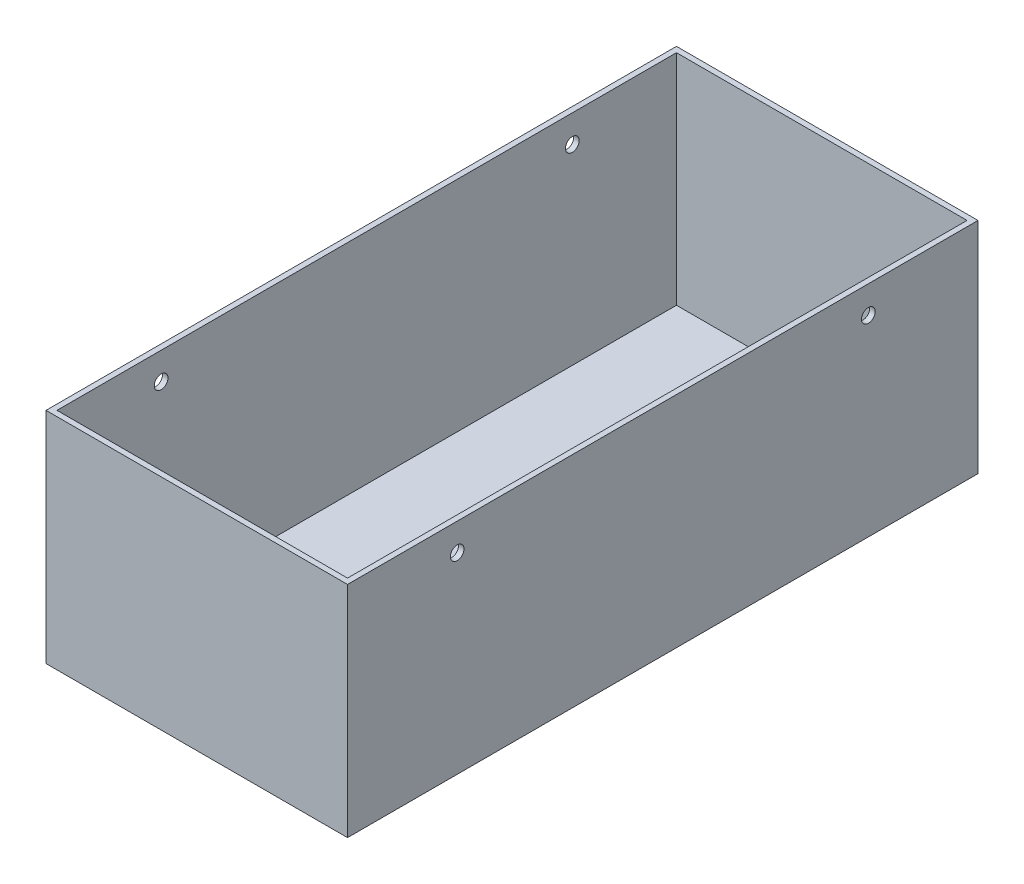
SolidWorks part; units mm, degrees
material "Mahogany"
ref_plane "Front Plane" through (0, 0, 0) normal (0, 0, 1) x (1, 0, 0)
ref_plane "Top Plane" through (0, 0, 0) normal (0, 1, 0) x (1, 0, 0)
ref_plane "Right Plane" through (0, 0, 0) normal (1, 0, 0) x (0, 0, -1)
sketch "Sketch4" plane through (0, 0, 0) normal (0, 1, 0) x (1, 0, 0)
  line L1 (62.5995, 198.4667) -> (172.5995, 198.4667)
  line L2 (62.5995, 198.4667) -> (62.5995, -31.5333)
  line L3 (62.5995, -31.5333) -> (172.5995, -31.5333)
  line L4 (172.5995, 198.4667) -> (172.5995, -31.5333)
extrude "Boss-Extrude3" add sketch "Sketch4" along normal blind 80
sketch "Sketch5" plane through (0, 80, 0) normal (0, 1, 0) x (1, 0, 0)
  line L0 (117.5995, -31.5333) -> (117.5995, -29.5333) construction
  line L5 (62.5995, -31.5333) -> (172.5995, -31.5333) construction
  line L6 (64.5995, -29.5333) -> (170.5995, -29.5333)
  line L7 (62.5995, 83.4667) -> (172.5995, 83.4667)
  line L8 (62.5995, 198.4667) -> (62.5995, -31.5333) construction
  line L9 (172.5995, -31.5333) -> (172.5995, 198.4667) construction
  line L10 (64.5995, 196.4667) -> (170.5995, 196.4667)
  line L11 (64.5995, 196.4667) -> (64.5995, -29.5333)
  line L12 (170.5995, -29.5333) -> (170.5995, 196.4667)
  point P7 (117.5995, -29.5333)
extrude "Cut-Extrude2" cut sketch "Sketch5" against normal blind 79.8 contours L7 L12 L10 L11 | L6 L12 L7 L11
sketch "Sketch6" plane through (62.5995, 0, 0) normal (-1, 0, 0) x (0, 0, 1)
  line L0 (-83.4667, 80) -> (-83.4667, 0) construction
  line L1 (-198.4667, 80) -> (31.5333, 80) construction
  line L2 (-198.4667, 0) -> (31.5333, 0) construction
  line L3 (31.5333, 80) -> (31.5333, 0) construction
  circle A0 centre (-8.4667, 70) radius 2.5
  circle A2 centre (-158.4667, 70) radius 2.5
  dimension "D1" = 10
  dimension "D2" = 40
extrude "Cut-Extrude3" cut sketch "Sketch6" against normal blind 130 contours A2 | A0
